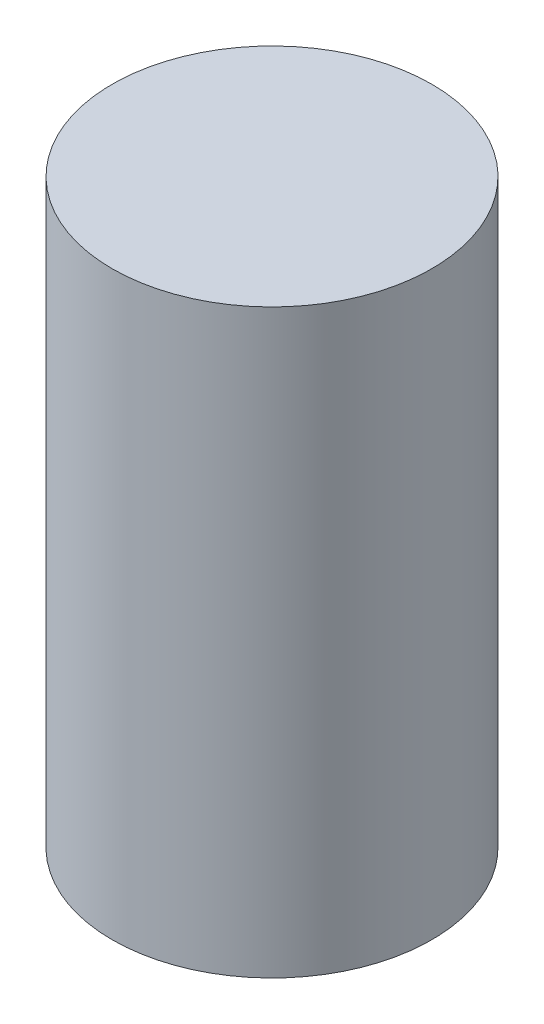
SolidWorks part; units mm, degrees
ref_plane "Front Plane" through (0, 0, 0) normal (0, 0, 1) x (1, 0, 0)
ref_plane "Top Plane" through (0, 0, 0) normal (0, 1, 0) x (1, 0, 0)
ref_plane "Right Plane" through (0, 0, 0) normal (1, 0, 0) x (0, 0, -1)
sketch "Sketch1" plane through (0, 0, 0) normal (0, 1, 0) x (1, 0, 0)
  circle A0 centre (0, 0) radius 69.85
  dimension "D1" = 139.7
extrude "Boss-Extrude1" add sketch "Sketch1" along normal blind 254
